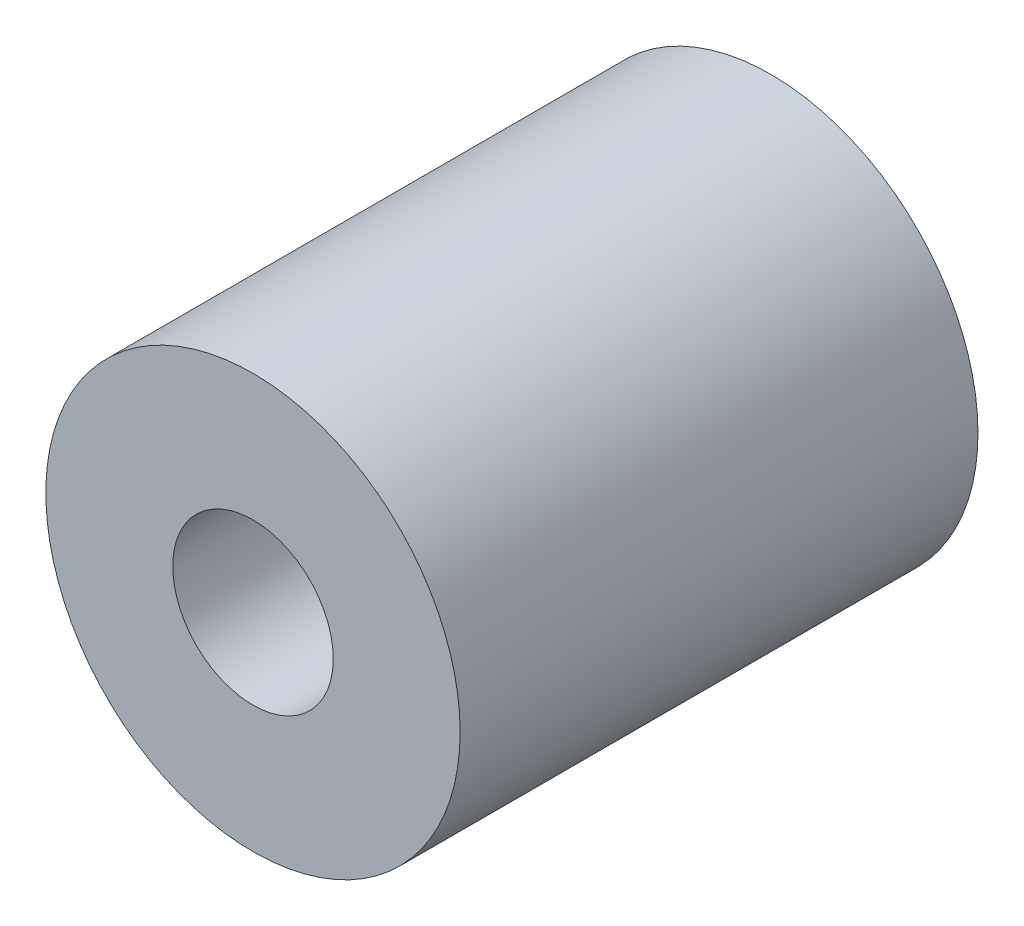
SolidWorks part; units mm, degrees
material "ABS"
ref_plane "前视基准面" through (0, 0, 0) normal (0, 0, 1) x (1, 0, 0)
ref_plane "上视基准面" through (0, 0, 0) normal (0, 1, 0) x (1, 0, 0)
ref_plane "右视基准面" through (0, 0, 0) normal (1, 0, 0) x (0, 0, -1)
sketch "草图1" plane through (0, 0, 0) normal (0, 0, 1) x (1, 0, 0)
  circle A0 centre (0, 0) radius 3.1
  circle A1 centre (0, 0) radius 8
extrude "凸台-拉伸1" add sketch "草图1" along normal mid plane 20
